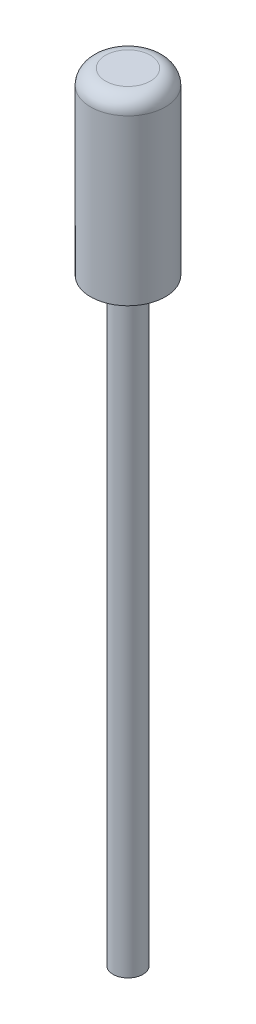
SolidWorks part; units mm, degrees
ref_plane "Front Plane" through (0, 0, 0) normal (0, 0, 1) x (1, 0, 0)
ref_plane "Top Plane" through (0, 0, 0) normal (0, 1, 0) x (1, 0, 0)
ref_plane "Right Plane" through (0, 0, 0) normal (1, 0, 0) x (0, 0, -1)
sketch "Sketch1" plane through (0, 0, 0) normal (0, 0, 1) x (1, 0, 0)
  line L0 (0, 0) -> (1, 0)
  line L1 (1, 0) -> (1, 39.6)
  line L2 (1.4, 40) -> (2.5, 40)
  line L3 (2.5, 40) -> (2.5, 51)
  line L4 (1.5, 52) -> (0, 52)
  line L5 (0, 52) -> (0, 0)
  arc A0 (2.5, 51) -> (1.5, 52) centre (1.5, 51) ccw
  arc A3 (1, 39.6) -> (1.4, 40) centre (1.4, 39.6) cw
  point P5 (0, 0)
  point P6 (0, 0)
  point P7 (2.5, 48.0909)
  point P8 (2.5, 40)
  point P9 (0.729, 40)
  point P12 (2.5, 52)
  point P15 (2.5, 40)
  point P18 (0, 52)
  point P20 (1, 40)
  dimension "D5" = 1
  dimension "D7" = 0.4
  dimension "D1" = 2.5
  dimension "D2" = 40
  dimension "D3" = 12
  dimension "D4" = 1
revolve "Revolve1" add sketch "Sketch1" angle 360 about L5
